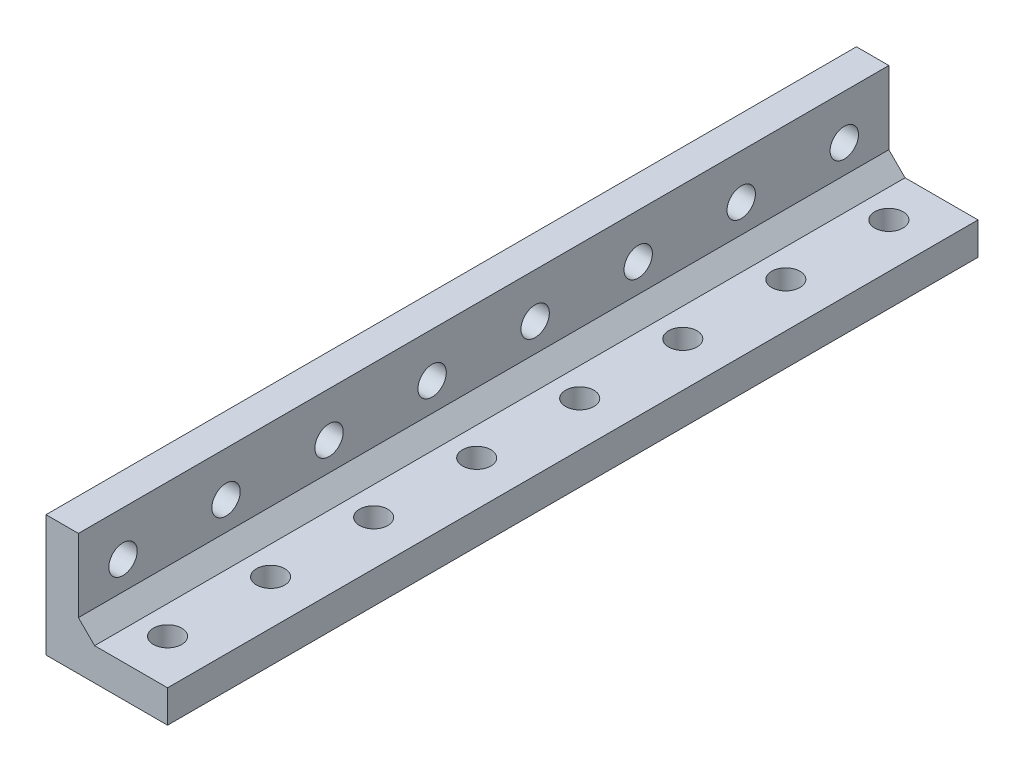
SolidWorks part; units mm, degrees
ref_plane "Plano frontal" through (0, 0, 0) normal (0, 0, 1) x (1, 0, 0)
ref_plane "Plano superior" through (0, 0, 0) normal (0, 1, 0) x (1, 0, 0)
ref_plane "Plano direito" through (0, 0, 0) normal (1, 0, 0) x (0, 0, -1)
sketch "Esboço1" plane through (0, 0, 0) normal (0, 0, 1) x (1, 0, 0)
  line L0 (0, 0) -> (0, 15)
  line L1 (0, 0) -> (15, 0)
  line L2 (15, 0) -> (15, 4)
  line L3 (15, 4) -> (4, 4)
  line L4 (4, 4) -> (4, 15)
  line L5 (4, 15) -> (0, 15)
  dimension "D1" = 4
  dimension "D2" = 4
  dimension "D3" = 15
  dimension "D4" = 15
extrude "Ressalto-extrusão1" add sketch "Esboço1" along normal blind 100
sketch "Esboço2" plane through (4, 0, 0) normal (1, 0, 0) x (0, 0, -1)
  line L0 (-100, 15) -> (0, 15) construction
  line L1 (-100, 4) -> (-100, 15) construction
  circle A0 centre (-94.5, 9.5) radius 1.75
  dimension "D1" = 3.5
  dimension "D2" = 5.5
  dimension "D3" = 5.5
extrude "Corte-extrusão1" cut sketch "Esboço2" against normal blind 100
pattern_linear "Padrão linear1" count 8 spacing 12.7143 along (0, 0, -1) of "Corte-extrusão1"
sketch "Esboço3" plane through (0, 4, 0) normal (0, 1, 0) x (1, 0, 0)
  line L0 (15, -100) -> (4, -100) construction
  line L1 (15, -100) -> (15, 0) construction
  circle A0 centre (9.5, -94.5) radius 1.75
  dimension "D1" = 3.5
  dimension "D2" = 5.5
  dimension "D3" = 5.5
extrude "Corte-extrusão2" cut sketch "Esboço3" against normal blind 100
pattern_linear "Padrão linear2" count 8 spacing 12.7143 along (0, 0, -1) of "Corte-extrusão2"
chamfer "Chanfro1" distance 2 angle 45 1 edges at (4, 4, 50)
